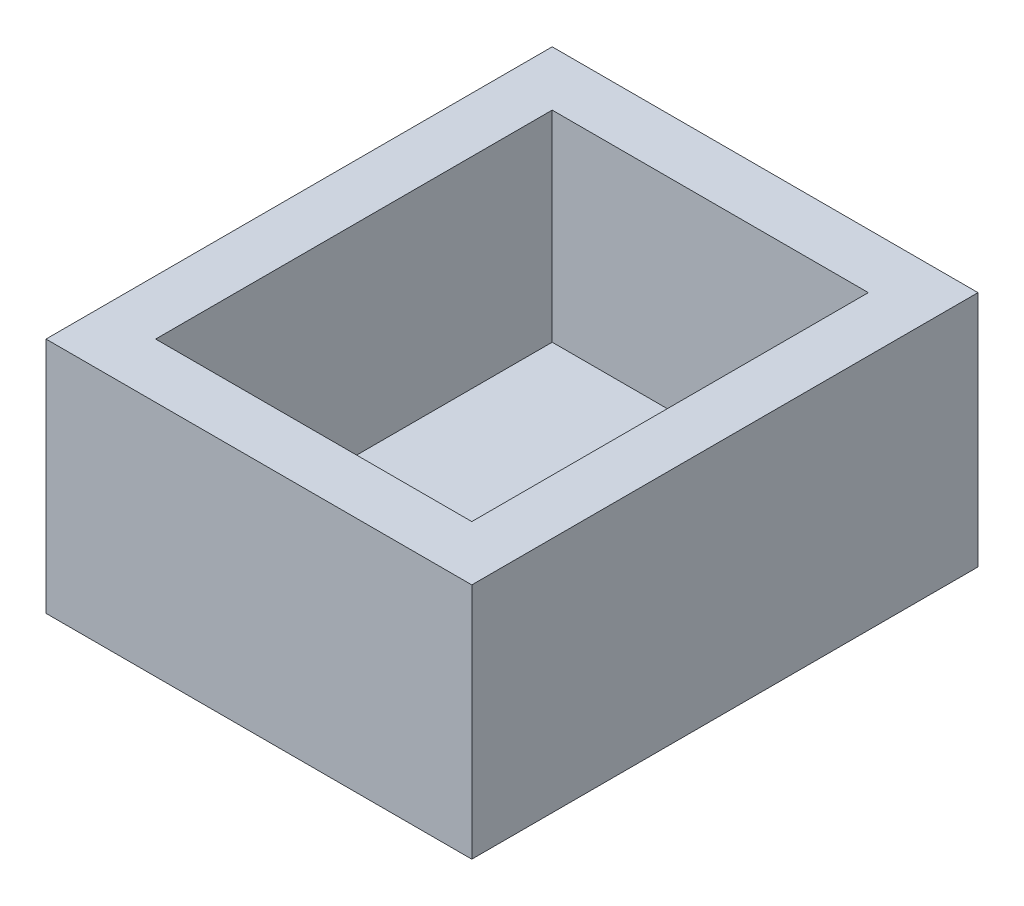
SolidWorks part; units mm, degrees
material "ABS"
ref_plane "Front Plane" through (0, 0, 0) normal (0, 0, 1) x (1, 0, 0)
ref_plane "Top Plane" through (0, 0, 0) normal (0, 1, 0) x (1, 0, 0)
ref_plane "Right Plane" through (0, 0, 0) normal (1, 0, 0) x (0, 0, -1)
sketch "Sketch1" plane through (0, 0, 0) normal (0, 1, 0) x (1, 0, 0)
  line L0 (-8.65, 19.8334) -> (-8.65, -1.8666)
  line L1 (-8.65, -1.8666) -> (8.65, -1.8666)
  line L2 (8.65, -1.8666) -> (8.65, 19.8334)
  line L3 (8.65, 19.8334) -> (-8.65, 19.8334)
  line L4 (-11.65, 22.8334) -> (-11.65, -4.8666)
  line L5 (-11.65, -4.8666) -> (11.65, -4.8666)
  line L6 (11.65, -4.8666) -> (11.65, 22.8334)
  line L7 (11.65, 22.8334) -> (-11.65, 22.8334)
  dimension "D2" = 8.65
  dimension "D3" = 8.65
  dimension "D4" = 19.8334
  dimension "D5" = 1.8666
  dimension "D1" = 3
extrude "Boss-Extrude1" add sketch "Sketch1" along normal blind 13
sketch "Sketch2" plane through (0, 0, 0) normal (0, -1, 0) x (1, 0, 0)
  line L9 (-8.65, 1.8666) -> (8.65, 1.8666)
  line L10 (-8.65, 1.8666) -> (-8.65, -19.8334)
  line L11 (-8.65, -19.8334) -> (8.65, -19.8334)
  line L12 (8.65, 1.8666) -> (8.65, -19.8334)
  circle A0 centre (6.24, -0.7079) radius 1.75
  dimension "D1" = 3.5
  dimension "D2" = 2.41
  dimension "D3" = 22.1255
extrude "Boss-Extrude2" add sketch "Sketch2" against normal blind 2
